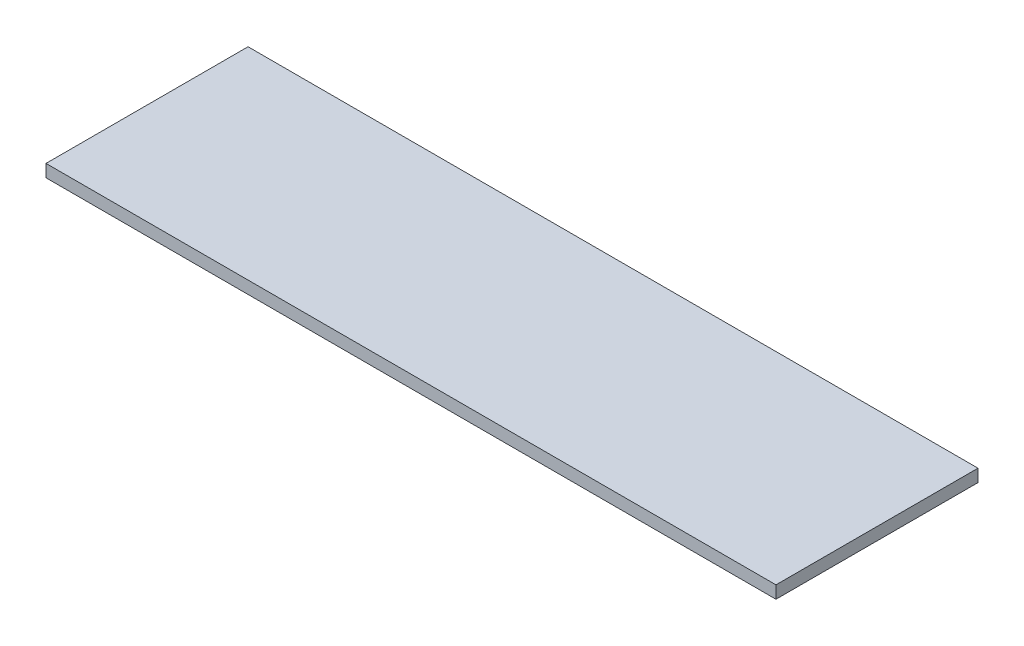
SolidWorks part; units mm, degrees
material "Cedar"
ref_plane "Front Plane" through (0, 0, 0) normal (0, 0, 1) x (1, 0, 0)
ref_plane "Top Plane" through (0, 0, 0) normal (0, 1, 0) x (1, 0, 0)
ref_plane "Right Plane" through (0, 0, 0) normal (1, 0, 0) x (0, 0, -1)
sketch "Sketch1" plane through (0, 0, 0) normal (0, 1, 0) x (1, 0, 0)
  line L1 (-533.4, -147.6375) -> (533.4, -147.6375)
  line L2 (-533.4, -147.6375) -> (-533.4, 147.6375)
  line L3 (-533.4, 147.6375) -> (533.4, 147.6375)
  line L4 (533.4, -147.6375) -> (533.4, 147.6375)
  line L5 (-533.4, -147.6375) -> (533.4, 147.6375) construction
  line L6 (-533.4, 147.6375) -> (533.4, -147.6375) construction
  point P0 (0, 0)
  dimension "D1" = 1066.8
  dimension "D2" = 295.275
extrude "Boss-Extrude1" add sketch "Sketch1" along normal blind 18.2562
